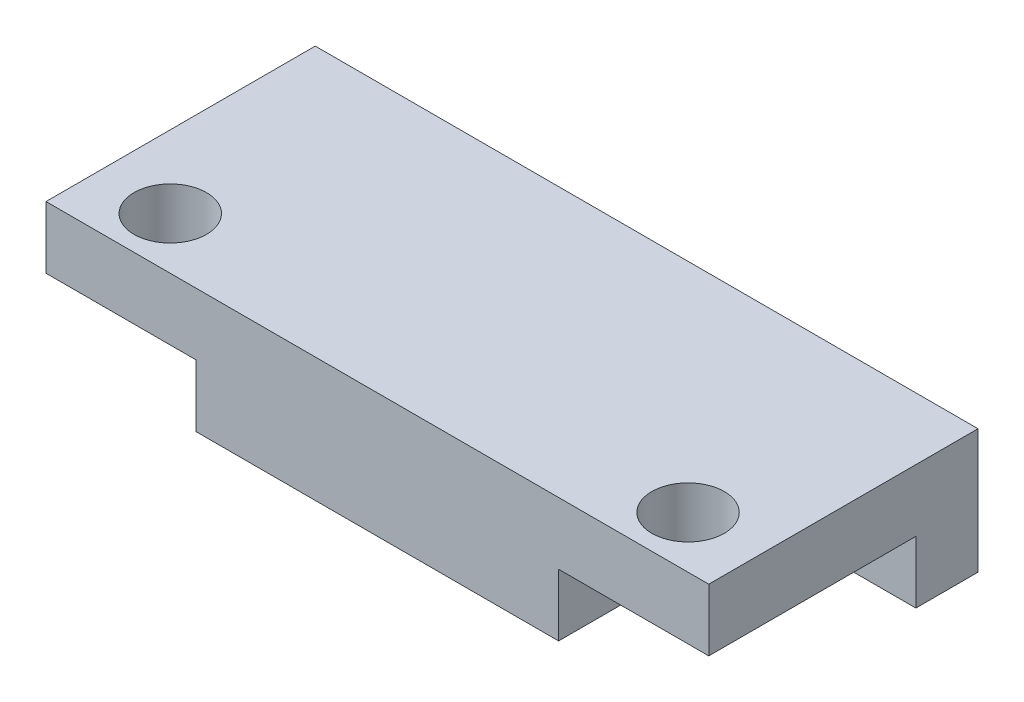
SolidWorks part; units mm, degrees
ref_plane "정면" through (0, 0, 0) normal (0, 0, 1) x (1, 0, 0)
ref_plane "윗면" through (0, 0, 0) normal (0, 1, 0) x (1, 0, 0)
ref_plane "우측면" through (0, 0, 0) normal (1, 0, 0) x (0, 0, -1)
sketch "스케치1" plane through (0, 0, 0) normal (0, 1, 0) x (1, 0, 0)
  line L0 (-74.6323, 0) -> (70.8129, 0) construction
  line L1 (0, 49.1871) -> (0, -55.6903) construction
  line L3 (16, -6.5) -> (-16, -6.5)
  line L4 (16, -6.5) -> (16, 6.5)
  line L5 (16, 6.5) -> (-16, 6.5)
  line L6 (-16, -6.5) -> (-16, 6.5)
  line L7 (16, -6.5) -> (-16, 6.5) construction
  line L8 (16, 6.5) -> (-16, -6.5) construction
  point P5 (0, 0)
  dimension "D1" = 32
  dimension "D2" = 13
extrude "보스-돌출1" add sketch "스케치1" along normal blind 3
sketch "스케치2" plane through (0, 3, 0) normal (0, 1, 0) x (1, 0, 0)
  line L0 (-16, 6.5) -> (-16, -6.5) construction
  line L2 (-16, -6.5) -> (16, -6.5) construction
  circle A0 centre (-12.5, -4) radius 1.75
  circle A1 centre (12.5, -4) radius 1.75
  point P8 (0, 0)
  dimension "D1" = 25
  dimension "D2" = 3.5
  dimension "D3" = 3.5
  dimension "D4" = 3.5
  dimension "D5" = 2.5
extrude "컷-돌출1" cut sketch "스케치2" against normal through all
sketch "스케치3" plane through (0, 0, 0) normal (0, -1, 0) x (1, 0, 0)
  line L0 (-16, 6.5) -> (16, 6.5) construction
  line L1 (-8.75, 6.5) -> (8.75, 6.5)
  line L2 (-8.75, 6.5) -> (-8.75, -3.5)
  line L4 (8.75, 6.5) -> (8.75, -3.5)
  line L6 (16, 6.5) -> (16, -6.5) construction
  line L8 (-16, -6.5) -> (-16, -3.5)
  line L9 (-16, -3.5) -> (-8.75, -3.5)
  line L15 (-16, -6.5) -> (16, -6.5)
  line L16 (16, -3.5) -> (16, -6.5)
  line L17 (8.75, -3.5) -> (16, -3.5)
  circle A0 centre (-12.5, 4) radius 1.75 construction
  circle A2 centre (12.5, 4) radius 1.75 construction
  point P13 (-8.75, -3.5)
  point P14 (8.75, -3.5)
  dimension "D1" = 2
  dimension "D2" = 2
  dimension "D4" = 3
extrude "보스-돌출2" add sketch "스케치3" along normal blind 3
